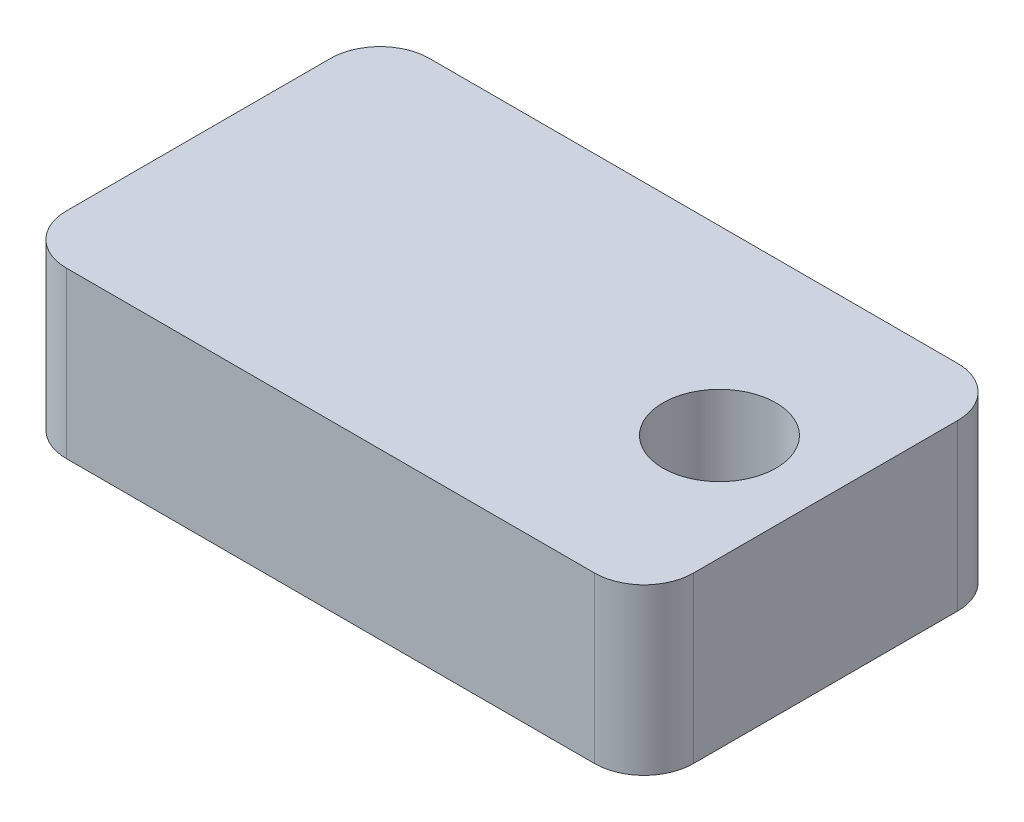
SolidWorks part; units mm, degrees
ref_plane "Front Plane" through (0, 0, 0) normal (0, 0, 1) x (1, 0, 0)
ref_plane "Top Plane" through (0, 0, 0) normal (0, 1, 0) x (1, 0, 0)
ref_plane "Right Plane" through (0, 0, 0) normal (1, 0, 0) x (0, 0, -1)
sketch "Sketch1" plane through (0, 0, 0) normal (0, 1, 0) x (1, 0, 0)
  line L1 (-19, 11) -> (19, 11)
  line L2 (-19, 11) -> (-19, -11)
  line L3 (-19, -11) -> (19, -11)
  line L4 (19, 11) -> (19, -11)
  line L5 (-19, 11) -> (19, -11) construction
  line L6 (-19, -11) -> (19, 11) construction
  circle A0 centre (12.571, 0) radius 3.429
  point P0 (0, 0)
  dimension "D4" = 6.858
  dimension "D1" = 38
  dimension "D2" = 22
  dimension "D3" = 6.429
extrude "Boss-Extrude1" add sketch "Sketch1" along normal blind 10
fillet "Fillet1" radius 3 4 edges at (-19, 5, -11) (19, 5, -11) (19, 5, 11) (-19, 5, 11)
